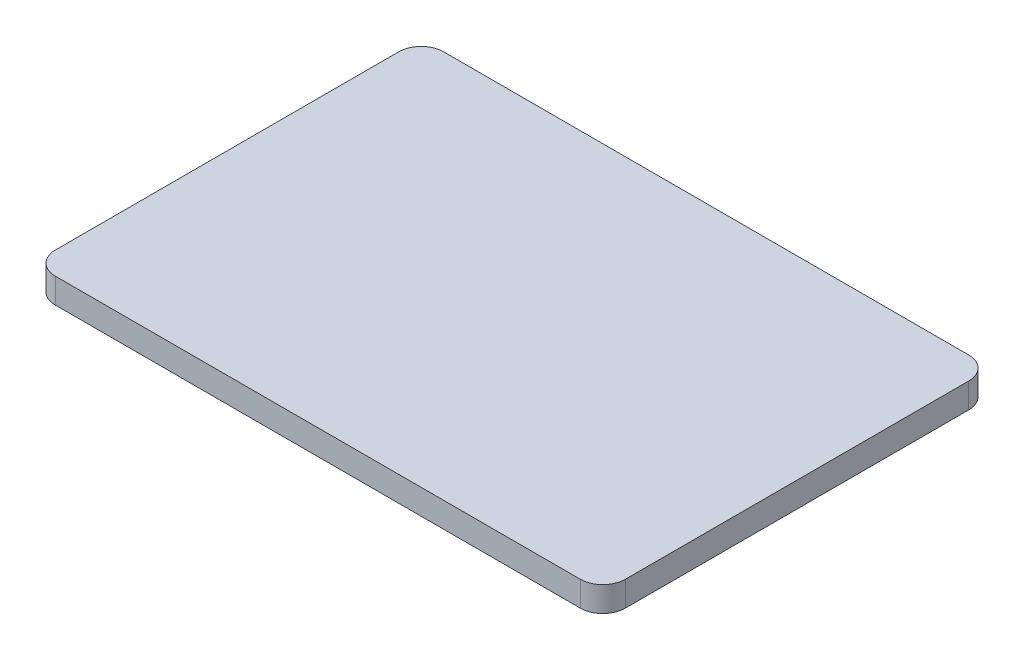
SolidWorks part; units mm, degrees
ref_plane "前视基准面" through (0, 0, 0) normal (0, 0, 1) x (1, 0, 0)
ref_plane "上视基准面" through (0, 0, 0) normal (0, 1, 0) x (1, 0, 0)
ref_plane "右视基准面" through (0, 0, 0) normal (1, 0, 0) x (0, 0, -1)
other "Configuration Table"
sketch "草图1" plane through (0, 0, 0) normal (0, 1, 0) x (1, 0, 0)
  line L1 (-20.95, 15.5) -> (20.95, 15.5)
  line L2 (-22.75, 13.7) -> (-22.75, -13.7)
  line L3 (-20.95, -15.5) -> (20.95, -15.5)
  line L4 (22.75, 13.7) -> (22.75, -13.7)
  line L5 (-22.75, 15.5) -> (22.75, -15.5) construction
  line L6 (-22.75, -15.5) -> (22.75, 15.5) construction
  arc A0 (-20.95, 15.5) -> (-22.75, 13.7) centre (-20.95, 13.7) ccw
  arc A1 (-22.75, -13.7) -> (-20.95, -15.5) centre (-20.95, -13.7) ccw
  arc A2 (20.95, -15.5) -> (22.75, -13.7) centre (20.95, -13.7) ccw
  arc A3 (20.95, 15.5) -> (22.75, 13.7) centre (20.95, 13.7) cw
  point P0 (0, 0)
  dimension "D3" = 1.8
  dimension "D1" = 45.5
  dimension "D2" = 31
extrude "凸台-拉伸1" add sketch "草图1" along normal blind 2
